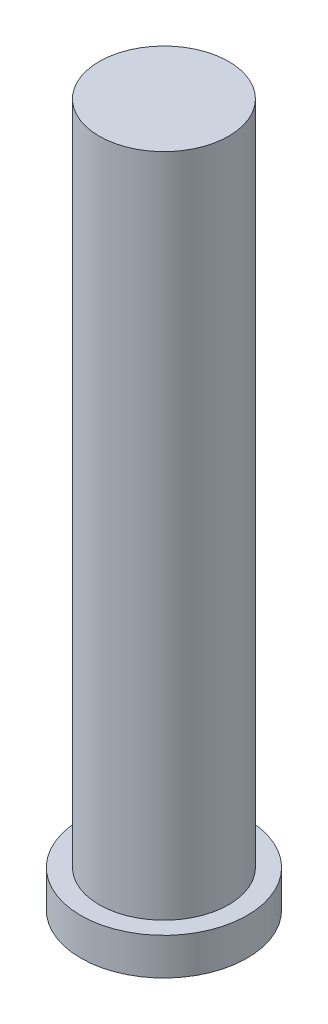
SolidWorks part; units mm, degrees
ref_plane "Front Plane" through (0, 0, 0) normal (0, 0, 1) x (1, 0, 0)
ref_plane "Top Plane" through (0, 0, 0) normal (0, 1, 0) x (1, 0, 0)
ref_plane "Right Plane" through (0, 0, 0) normal (1, 0, 0) x (0, 0, -1)
sketch "Sketch1" plane through (0, 0, 0) normal (0, 1, 0) x (1, 0, 0)
  circle A0 centre (0, 0) radius 2.8575
  dimension "D1" = 5.715
extrude "Boss-Extrude1" add sketch "Sketch1" along normal blind 1.27
sketch "Sketch2" plane through (0, 1.27, 0) normal (0, 1, 0) x (1, 0, 0)
  circle A0 centre (0, 0) radius 2.2225
  dimension "D1" = 4.445
extrude "Boss-Extrude2" add sketch "Sketch2" along normal blind 22.86
